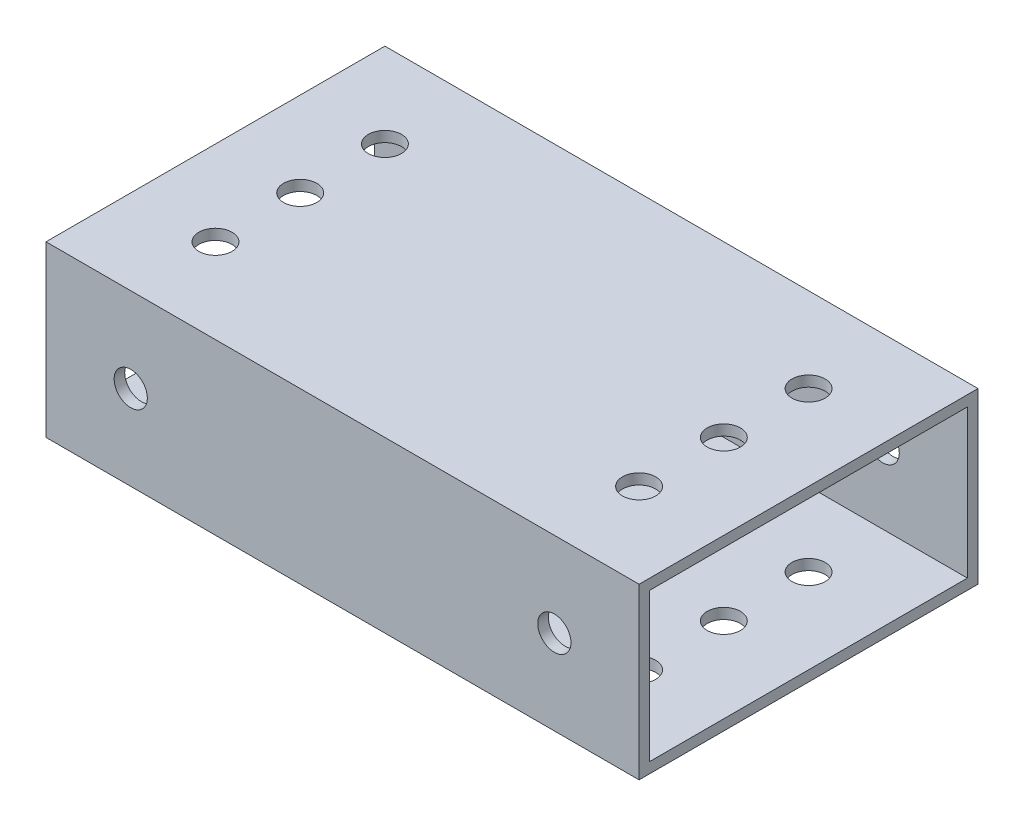
SolidWorks part; units mm, degrees
material "6061-T6 (SS)"
ref_plane "Front Plane" through (0, 0, 0) normal (0, 0, 1) x (1, 0, 0)
ref_plane "Top Plane" through (0, 0, 0) normal (0, 1, 0) x (1, 0, 0)
ref_plane "Right Plane" through (0, 0, 0) normal (1, 0, 0) x (0, 0, -1)
sketch "Sketch1" plane through (0, 0, 0) normal (1, 0, 0) x (0, 0, -1)
  line L1 (0, 0) -> (50.8, 0)
  line L2 (0, 0) -> (0, 25.4)
  line L3 (0, 25.4) -> (50.8, 25.4)
  line L4 (50.8, 0) -> (50.8, 25.4)
  dimension "D1" = 25.4
  dimension "D2" = 50.8
extrude "Boss-Extrude1" add sketch "Sketch1" along normal mid plane 88.9
shell "Shell1" thickness 1.5875
sketch "Sketch2" plane through (0, 25.4, 0) normal (0, 1, 0) x (1, 0, 0)
  line L0 (-31.75, 50.8) -> (-31.75, 0) construction
  line L1 (44.45, 50.8) -> (-44.45, 50.8) construction
  line L2 (44.45, 0) -> (-44.45, 0) construction
  line L3 (-44.45, 50.8) -> (-44.45, 0) construction
  circle A0 centre (-31.75, 25.4) radius 2.4892
  circle A1 centre (-31.75, 12.7) radius 2.4892
  circle A2 centre (-31.75, 38.1) radius 2.4892
  dimension "D1" = 4.9784
  dimension "D2" = 12.7
  dimension "D3" = 12.7
  dimension "D4" = 12.7
extrude "Cut-Extrude1" cut sketch "Sketch2" against normal through all
sketch "Sketch3" plane through (0, 0, 0) normal (0, 0, 1) x (1, 0, 0)
  line L0 (44.45, 25.4) -> (-44.45, 25.4) construction
  line L1 (-44.45, 25.4) -> (-44.45, 0) construction
  circle A0 centre (-31.75, 12.7) radius 2.4892
  dimension "D3" = 4.9784
  dimension "D1" = 12.7
  dimension "D2" = 12.7
extrude "Cut-Extrude2" cut sketch "Sketch3" against normal through all
mirror "Mirror1" about plane through (0, 0, 0) normal (1, 0, 0) of "Cut-Extrude2", "Cut-Extrude1"
